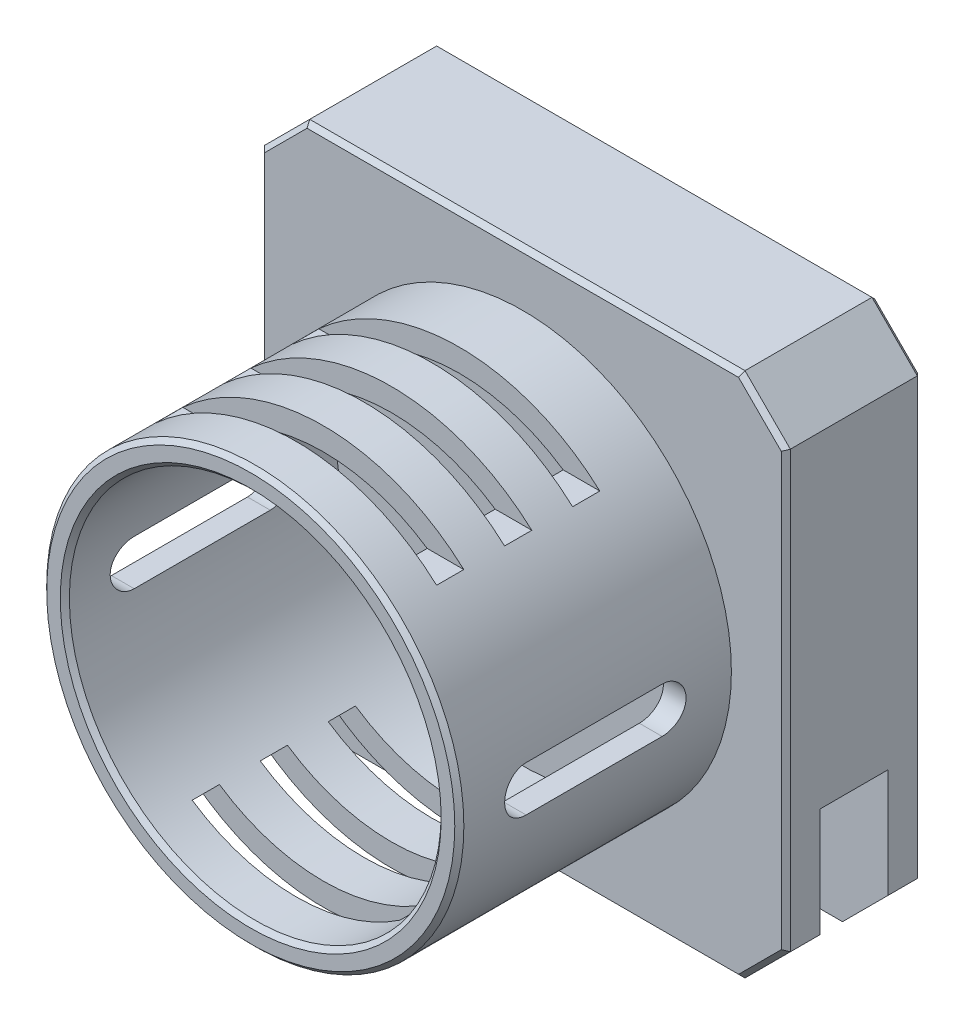
SolidWorks part; units mm, degrees
ref_plane "Ebene vorne" through (0, 0, 0) normal (0, 0, 1) x (1, 0, 0)
ref_plane "Ebene oben" through (0, 0, 0) normal (0, 1, 0) x (1, 0, 0)
ref_plane "Ebene rechts" through (0, 0, 0) normal (1, 0, 0) x (0, 0, -1)
sketch "Skizze3" plane through (0, 0, 0) normal (0, 0, 1) x (1, 0, 0)
  line L1 (-29, 29) -> (29, 29)
  line L2 (-29, 29) -> (-29, -29)
  line L3 (-29, -29) -> (29, -29)
  line L4 (29, 29) -> (29, -29)
  line L5 (-29, 29) -> (29, -29) construction
  line L6 (-29, -29) -> (29, 29) construction
  point P0 (0, 0)
extrude "Aufsatz-Linear austragen1" add sketch "Skizze3" along normal blind 15
sketch "Skizze4" plane through (0, 0, 0) normal (0, 0, -1) x (-1, 0, 0)
  line L0 (-29, 0) -> (29, 0) construction
  line L1 (-29, -29) -> (-29, 29) construction
  line L2 (29, 29) -> (29, -29) construction
  line L3 (0, 29) -> (0, -29) construction
  line L4 (-29, 29) -> (29, 29) construction
  line L5 (29, -29) -> (-29, -29) construction
  circle A0 centre (0, 19) radius 7.5
  circle A1 centre (19, -19) radius 7.5
  circle A2 centre (-19, -19) radius 7.5
  dimension "D1" = 38
  dimension "D2" = 38
  dimension "D3" = 38
extrude "Aufsatz-Linear austragen2" add sketch "Skizze4" along normal blind 2
chamfer "Fase1" distance 5 angle 45 4 edges at (-29, -29, 7.5) (29, -29, 7.5) (29, 29, 7.5) (-29, 29, 7.5)
sketch "Skizze5" plane through (0, 0, 15) normal (0, 0, 1) x (1, 0, 0)
  circle A0 centre (0, 0) radius 20.5
  circle A1 centre (0, 0) radius 23
extrude "Aufsatz-Linear austragen3" add sketch "Skizze5" along normal blind 30
ref_plane "Ebene1" through (0, -23, 0) normal (0, -1, 0) x (0, 0, -1)
sketch "Skizze6" plane through (0, -23, 0) normal (0, -1, 0) x (0, 0, -1)
  line L0 (-45, 23) -> (-45, -23) construction
  line L1 (-25, 19.7603) -> (-22, 19.7603)
  line L2 (-25, 19.7603) -> (-25, -19.7603)
  line L3 (-25, -19.7603) -> (-22, -19.7603)
  line L4 (-22, 19.7603) -> (-22, -19.7603)
  line L5 (-25, 19.7603) -> (-22, -19.7603) construction
  line L6 (-25, -19.7603) -> (-22, 19.7603) construction
  line L7 (-32.5, 19.7603) -> (-29.5, 19.7603)
  line L8 (-32.5, 19.7603) -> (-32.5, -19.7603)
  line L9 (-32.5, -19.7603) -> (-29.5, -19.7603)
  line L10 (-29.5, 19.7603) -> (-29.5, -19.7603)
  line L11 (-32.5, 19.7603) -> (-29.5, -19.7603) construction
  line L12 (-32.5, -19.7603) -> (-29.5, 19.7603) construction
  line L13 (-40, 19.7603) -> (-37, 19.7603)
  line L14 (-40, 19.7603) -> (-40, -19.7603)
  line L15 (-40, -19.7603) -> (-37, -19.7603)
  line L16 (-37, 19.7603) -> (-37, -19.7603)
  line L17 (-40, 19.7603) -> (-37, -19.7603) construction
  line L18 (-40, -19.7603) -> (-37, 19.7603) construction
  point P0 (-23.5, 0)
  point P5 (-31, 0)
  point P10 (-38.5, 0)
  dimension "D1" = 3
  dimension "D2" = 3
  dimension "D3" = 3
  dimension "D4" = 6.5
  dimension "D5" = 14
  dimension "D6" = 21.5
extrude "Schnitt-Linear austragen1" cut sketch "Skizze6" against normal blind 6
ref_plane "Ebene2" through (0, 23, 0) normal (0, 1, 0) x (0, 0, -1)
sketch "Skizze7" plane through (0, 23, 0) normal (0, 1, 0) x (0, 0, -1)
  line L0 (-45, 23) -> (-45, -23) construction
  line L1 (-25, 17.5647) -> (-22, 17.5647)
  line L2 (-25, 17.5647) -> (-25, -17.5647)
  line L3 (-25, -17.5647) -> (-22, -17.5647)
  line L4 (-22, 17.5647) -> (-22, -17.5647)
  line L5 (-25, 17.5647) -> (-22, -17.5647) construction
  line L6 (-25, -17.5647) -> (-22, 17.5647) construction
  line L7 (-32.5, 17.5647) -> (-29.5, 17.5647)
  line L8 (-32.5, 17.5647) -> (-32.5, -17.5647)
  line L9 (-32.5, -17.5647) -> (-29.5, -17.5647)
  line L10 (-29.5, 17.5647) -> (-29.5, -17.5647)
  line L11 (-32.5, 17.5647) -> (-29.5, -17.5647) construction
  line L12 (-32.5, -17.5647) -> (-29.5, 17.5647) construction
  line L13 (-40, 17.5647) -> (-37, 17.5647)
  line L14 (-40, 17.5647) -> (-40, -17.5647)
  line L15 (-40, -17.5647) -> (-37, -17.5647)
  line L16 (-37, 17.5647) -> (-37, -17.5647)
  line L17 (-40, 17.5647) -> (-37, -17.5647) construction
  line L18 (-40, -17.5647) -> (-37, 17.5647) construction
  point P0 (-23.5, 0)
  point P5 (-31, 0)
  point P10 (-38.5, 0)
  dimension "D1" = 6.5
  dimension "D2" = 14
  dimension "D3" = 21.5
extrude "Schnitt-Linear austragen2" cut sketch "Skizze7" against normal blind 6
ref_plane "Ebene3" through (23, 0, 0) normal (1, 0, 0) x (0, 0, -1)
sketch "Skizze8" plane through (23, 0, 0) normal (1, 0, 0) x (0, 0, -1)
  line L0 (-37.5, 0) -> (-22.5, 0) construction
  line L1 (-37.5, 2.5) -> (-22.5, 2.5)
  line L2 (-37.5, -2.5) -> (-22.5, -2.5)
  line L3 (-45, 23) -> (-45, -23) construction
  arc A0 (-37.5, 2.5) -> (-37.5, -2.5) centre (-37.5, 0) ccw
  arc A1 (-22.5, -2.5) -> (-22.5, 2.5) centre (-22.5, 0) ccw
  point P3 (-30, 0)
  dimension "D1" = 7.5
extrude "Schnitt-Linear austragen3" cut sketch "Skizze8" against normal through all
chamfer "Fase2" distance 0.5 angle 45 5 edges at (23, 0, 45) (-7.5, 19, -2) (-26.5, -19, -2) (26.5, -19, -2) (20.5, 0, 45)
chamfer "Fase3" distance 0.5 angle 45 16 edges at (26.5, -26.5, 0) (29, 0, 0) (26.5, 26.5, 0) (0, 29, 0) (-26.5, 26.5, 0) (-29, 0, 0) (-26.5, -26.5, 0) (0, -29, 0) (-26.5, 26.5, 15) (0, 29, 15) (26.5, 26.5, 15) (29, 0, 15) (26.5, -26.5, 15) (0, -29, 15) (-26.5, -26.5, 15) (-29, 0, 15)
sketch "Skizze10" plane through (0, -29, 0) normal (0, -1, 0) x (1, 0, 0)
  line L0 (-7, -2) -> (7, -2) construction
  line L1 (-29.3876, 11.25) -> (29.3876, 11.25)
  line L2 (-29.3876, 11.25) -> (-29.3876, 3.75)
  line L3 (-29.3876, 3.75) -> (29.3876, 3.75)
  line L4 (29.3876, 11.25) -> (29.3876, 3.75)
  line L5 (-29.3876, 11.25) -> (29.3876, 3.75) construction
  line L6 (-29.3876, 3.75) -> (29.3876, 11.25) construction
  point P0 (0, 7.5)
  dimension "D1" = 7.5
  dimension "D2" = 9.5
extrude "Schnitt-Linear austragen5" cut sketch "Skizze10" against normal blind 17
